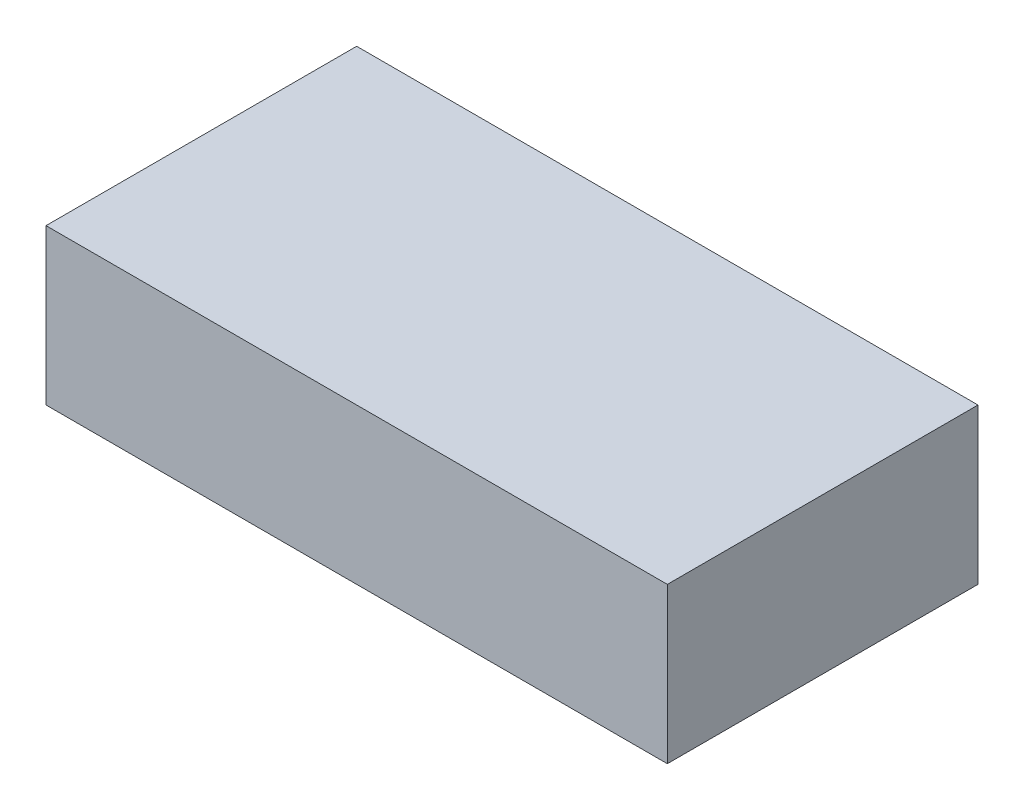
SolidWorks part; units mm, degrees
ref_plane "Plan de face" through (0, 0, 0) normal (0, 0, 1) x (1, 0, 0)
ref_plane "Plan de dessus" through (0, 0, 0) normal (0, 1, 0) x (1, 0, 0)
ref_plane "Plan de droite" through (0, 0, 0) normal (1, 0, 0) x (0, 0, -1)
sketch "Esquisse1" plane through (0, 0, 0) normal (0, 0, 1) x (1, 0, 0)
  line L1 (0, 0) -> (20, 0)
  line L2 (0, 0) -> (0, -5)
  line L3 (0, -5) -> (20, -5)
  line L4 (20, 0) -> (20, -5)
  dimension "D1" = 20
  dimension "D2" = 5
extrude "Boss.-Extru.1" add sketch "Esquisse1" along normal blind 10
